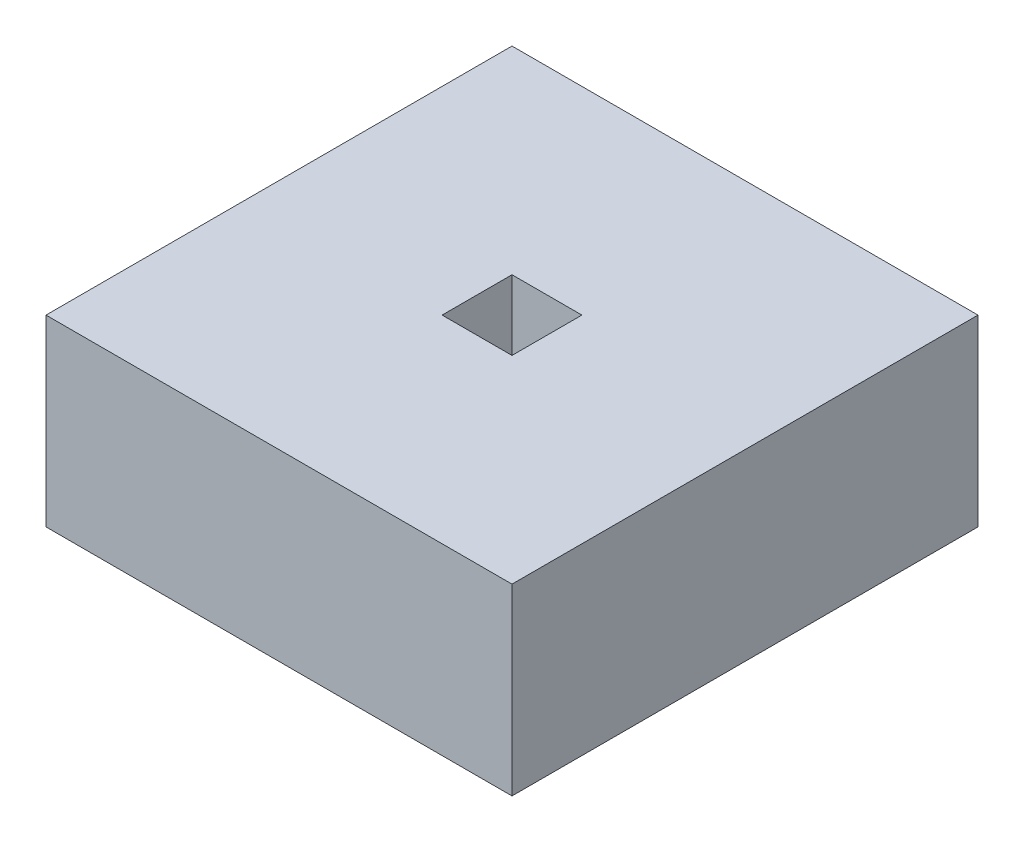
SolidWorks part; units mm, degrees
ref_plane "Front Plane" through (0, 0, 0) normal (0, 0, 1) x (1, 0, 0)
ref_plane "Top Plane" through (0, 0, 0) normal (0, 1, 0) x (1, 0, 0)
ref_plane "Right Plane" through (0, 0, 0) normal (1, 0, 0) x (0, 0, -1)
sketch "Sketch1" plane through (0, 0, 0) normal (0, 1, 0) x (1, 0, 0)
  line L1 (19.05, -19.05) -> (-19.05, -19.05)
  line L2 (19.05, -19.05) -> (19.05, 19.05)
  line L3 (19.05, 19.05) -> (-19.05, 19.05)
  line L4 (-19.05, -19.05) -> (-19.05, 19.05)
  line L5 (19.05, -19.05) -> (-19.05, 19.05) construction
  line L6 (19.05, 19.05) -> (-19.05, -19.05) construction
  line L7 (127, -127) -> (-127, -127)
  line L8 (127, -127) -> (127, 127)
  line L9 (127, 127) -> (-127, 127)
  line L10 (-127, -127) -> (-127, 127)
  line L11 (127, -127) -> (-127, 127) construction
  line L12 (127, 127) -> (-127, -127) construction
  point P0 (0, 0)
  point P6 (0, 0)
  dimension "D1" = 38.1
  dimension "D3" = 254
extrude "Boss-Extrude1" add sketch "Sketch1" along normal blind 100
ref_plane "Plane1" through (0, 99, 0) normal (0, 1, 0) x (1, 0, 0)
sketch "Sketch2" plane through (0, 99, 0) normal (0, 1, 0) x (1, 0, 0)
  line L14 (-126, -126) -> (126, -126)
  line L15 (126, -126) -> (126, 126)
  line L16 (126, 126) -> (-126, 126)
  line L17 (-126, 126) -> (-126, -126)
  line L18 (-126, -126) -> (126, -126)
  line L19 (126, -126) -> (126, 126)
  line L20 (126, 126) -> (-126, 126)
  line L21 (-126, 126) -> (-126, -126)
  line L32 (20.05, -20.05) -> (20.05, 20.05)
  line L33 (-20.05, -20.05) -> (20.05, -20.05)
  line L34 (-20.05, 20.05) -> (-20.05, -20.05)
  line L35 (20.05, 20.05) -> (-20.05, 20.05)
  line L36 (20.05, -20.05) -> (20.05, 20.05)
  line L37 (-20.05, -20.05) -> (20.05, -20.05)
  line L38 (-20.05, 20.05) -> (-20.05, -20.05)
  line L39 (20.05, 20.05) -> (-20.05, 20.05)
  dimension "D1" = 1
  dimension "D2" = 1
extrude "Cut-Extrude1" cut sketch "Sketch2" against normal offset from surface (98 mm away) 1 up to face at (0, 0, 0)
